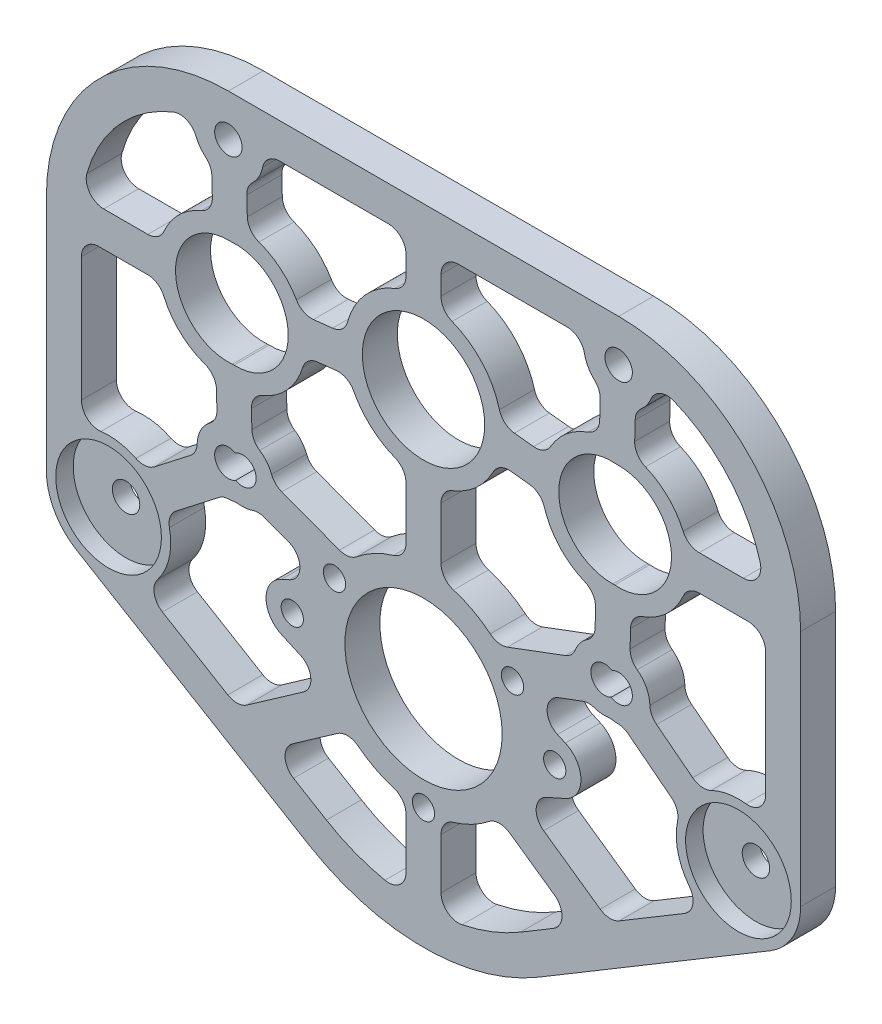
SolidWorks part; units mm, degrees
ref_plane "Front Plane" through (0, 0, 0) normal (0, 0, 1) x (1, 0, 0)
ref_plane "Top Plane" through (0, 0, 0) normal (0, 1, 0) x (1, 0, 0)
ref_plane "Right Plane" through (0, 0, 0) normal (1, 0, 0) x (0, 0, -1)
ref_plane "Plane1" through (0, 0, 3.175) normal (0, 0, 1) x (1, 0, 0)
sketch "Sketch1" plane through (0, 0, 3.175) normal (0, 0, 1) x (1, 0, 0)
  line L0 (0, -94.4087) -> (68.4315, -53.4351)
  line L1 (68.4315, -53.4351) -> (68.4315, 29.21)
  line L2 (68.4315, 29.21) -> (-68.4315, 29.21)
  line L3 (-68.4315, 29.21) -> (-68.4315, -53.4351)
  line L4 (-68.4315, -53.4351) -> (0, -94.4087)
extrude "Boss-Extrude1" add sketch "Sketch1" against normal blind 6.35
hole_wizard "M18 Clearance Hole1" positions "Sketch3" profile "Sketch2" hole size "M18" standard "ANSI Metric"
sketch "Sketch3" plane through (0, 0, 3.175) normal (0, 0, 1) x (1, 0, 0)
  point P0 (34.1324, -3.7778)
sketch "Sketch2" plane through (34.1324, -3.7778, 3.175) normal (1, 0, 0) x (0, -1, 0)
  line L0 (0, 0) -> (0, 6.35)
  line L1 (0, 6.35) -> (9.5885, 6.35)
  line L2 (9.5885, 6.35) -> (9.5885, 0)
  line L5 (9.5885, 0) -> (0, 0)
  line L10 (0, 6.35) -> (-9.5885, 6.35) construction
  line L11 (0, -6.35) -> (0, 107.95) construction
  dimension "Hole Dia." = 19.177
  dimension "Hole Depth" = 6.35
  dimension "Drill Angle" = 180
hole_wizard "M18 Clearance Hole2" positions "Sketch5" profile "Sketch4" hole size "M18" standard "ANSI Metric"
sketch "Sketch5" plane through (0, 0, 3.175) normal (0, 0, 1) x (1, 0, 0)
  point P0 (-34.1324, -3.7778)
sketch "Sketch4" plane through (-34.1324, -3.7778, 3.175) normal (1, 0, 0) x (0, -1, 0)
  line L0 (0, 0) -> (0, 6.35)
  line L1 (0, 6.35) -> (9.5885, 6.35)
  line L2 (9.5885, 6.35) -> (9.5885, 0)
  line L5 (9.5885, 0) -> (0, 0)
  line L10 (0, 6.35) -> (-9.5885, 6.35) construction
  line L11 (0, -6.35) -> (0, 107.95) construction
  dimension "Hole Dia." = 19.177
  dimension "Hole Depth" = 6.35
  dimension "Drill Angle" = 180
sketch "Sketch6" plane through (0, 0, 3.175) normal (0, 0, 1) x (1, 0, 0)
  line L0 (17.6151, -76.4604) -> (23.5825, -72.8874)
  line L1 (23.7726, -67.5625) -> (13.5655, -60.4154)
  line L2 (3.175, -65.8244) -> (3.175, -81.1835)
  arc A0 (3.175, -81.1835) -> (17.6151, -76.4604) centre (0, -47.0408) ccw
  arc A1 (23.5825, -72.8874) -> (23.7726, -67.5625) centre (21.9515, -70.1633) ccw
  arc A2 (13.5655, -60.4154) -> (3.175, -65.8244) centre (0, -47.0408) cw
extrude "Cut-Extrude1" cut sketch "Sketch6" against normal through all
sketch "Sketch7" plane through (0, 0, 3.175) normal (0, 0, 1) x (1, 0, 0)
  line L0 (31.913, 8.7913) -> (32.099, 16.1725)
  line L1 (29.1898, 22.86) -> (3.175, 22.86)
  line L2 (3.175, 22.86) -> (3.175, 13.9172)
  line L3 (14.1795, 1.6468) -> (22.2069, 0.7709)
  arc A0 (22.2069, 0.7709) -> (31.913, 8.7913) centre (34.1324, -3.7778) cw
  arc A1 (32.099, 16.1725) -> (29.1898, 22.86) centre (35.4115, 21.59) cw
  arc A2 (3.175, 13.9172) -> (14.1795, 1.6468) centre (0, 0) cw
extrude "Cut-Extrude2" cut sketch "Sketch7" against normal through all
sketch "Sketch8" plane through (0, 0, 3.175) normal (0, 0, 1) x (1, 0, 0)
  line L0 (13.4359, -33.536) -> (27.2428, -28.3669)
  line L1 (31.0928, -23.7619) -> (31.2829, -16.2191)
  line L2 (21.4909, -5.5387) -> (13.4908, -4.6658)
  line L3 (3.175, -13.9172) -> (3.175, -28.2572)
  arc A0 (3.175, -28.2572) -> (13.4359, -33.536) centre (0, -47.0408) cw
  arc A1 (27.2428, -28.3669) -> (31.0928, -23.7619) centre (32.8532, -29.1455) cw
  arc A2 (31.2829, -16.2191) -> (21.4909, -5.5387) centre (34.1324, -3.7778) cw
  arc A3 (13.4908, -4.6658) -> (3.175, -13.9172) centre (0, 0) cw
extrude "Cut-Extrude3" cut sketch "Sketch8" against normal through all
sketch "Sketch9" plane through (0, 0, 3.175) normal (0, 0, 1) x (1, 0, 0)
  line L0 (62.0815, -6.985) -> (47.776, -6.9766)
  line L1 (37.6309, -16.3791) -> (37.4408, -23.9218)
  line L2 (40.9401, -30.442) -> (50.5443, -37.8955)
  line L3 (62.0815, -36.8942) -> (62.0815, -6.985)
  arc A0 (47.776, -6.9766) -> (37.6309, -16.3791) centre (35.4115, -3.81) cw
  arc A1 (37.4408, -23.9218) -> (40.9401, -30.442) centre (35.4115, -29.21) cw
  arc A2 (50.5443, -37.8955) -> (62.0815, -36.8942) centre (57.15, -47.0408) cw
extrude "Cut-Extrude4" cut sketch "Sketch9" against normal through all
sketch "Sketch10" plane through (0, 0, 3.175) normal (0, 0, 1) x (1, 0, 0)
  line L0 (47.7716, -0.6266) -> (58.0296, -0.6326)
  line L1 (38.447, 16.0125) -> (38.261, 8.6314)
  arc A0 (38.261, 8.6314) -> (47.7716, -0.6266) centre (35.4115, -3.81) cw
  arc A1 (58.0296, -0.6326) -> (61.0882, 3.4008) centre (58.0315, 2.5424) ccw
  arc A2 (61.0882, 3.4008) -> (41.7412, 22.098) centre (35.4115, -3.81) ccw
  arc A3 (41.7412, 22.098) -> (38.447, 16.0125) centre (35.4115, 21.59) cw
extrude "Cut-Extrude5" cut sketch "Sketch10" against normal through all
sketch "Sketch11" plane through (0, 0, 3.175) normal (0, 0, 1) x (1, 0, 0)
  line L0 (-32.099, 16.1725) -> (-31.913, 8.7913)
  line L1 (-22.2069, 0.7709) -> (-14.1795, 1.6468)
  line L2 (-3.175, 13.9172) -> (-3.175, 22.86)
  line L3 (-3.175, 22.86) -> (-29.1898, 22.86)
  arc A0 (-29.1898, 22.86) -> (-32.099, 16.1725) centre (-35.4115, 21.59) cw
  arc A1 (-31.913, 8.7913) -> (-22.2069, 0.7709) centre (-34.1324, -3.7778) cw
  arc A2 (-14.1795, 1.6468) -> (-3.175, 13.9172) centre (0, 0) cw
extrude "Cut-Extrude6" cut sketch "Sketch11" against normal through all
sketch "Sketch12" plane through (0, 0, 3.175) normal (0, 0, 1) x (1, 0, 0)
  line L0 (-47.776, -6.9766) -> (-62.0815, -6.985)
  line L1 (-62.0815, -6.985) -> (-62.0815, -36.8942)
  line L2 (-50.5443, -37.8955) -> (-40.9401, -30.442)
  line L3 (-37.4408, -23.9218) -> (-37.6309, -16.3791)
  arc A0 (-37.6309, -16.3791) -> (-47.776, -6.9766) centre (-35.4115, -3.81) cw
  arc A1 (-62.0815, -36.8942) -> (-50.5443, -37.8955) centre (-57.15, -47.0408) cw
  arc A2 (-40.9401, -30.442) -> (-37.4408, -23.9218) centre (-35.4115, -29.21) cw
extrude "Cut-Extrude7" cut sketch "Sketch12" against normal through all
sketch "Sketch13" plane through (0, 0, 3.175) normal (0, 0, 1) x (1, 0, 0)
  line L0 (-38.261, 8.6314) -> (-38.447, 16.0125)
  line L1 (-58.0296, -0.6326) -> (-47.7716, -0.6266)
  arc A0 (-47.7716, -0.6266) -> (-38.261, 8.6314) centre (-35.4115, -3.81) cw
  arc A1 (-38.447, 16.0125) -> (-41.7412, 22.098) centre (-35.4115, 21.59) cw
  arc A2 (-41.7412, 22.098) -> (-61.0882, 3.4008) centre (-35.4115, -3.81) ccw
  arc A3 (-61.0882, 3.4008) -> (-58.0296, -0.6326) centre (-58.0315, 2.5424) ccw
extrude "Cut-Extrude8" cut sketch "Sketch13" against normal through all
sketch "Sketch14" plane through (0, 0, 3.175) normal (0, 0, 1) x (1, 0, 0)
  line L0 (-27.2428, -28.3669) -> (-13.4359, -33.536)
  line L1 (-3.175, -28.2572) -> (-3.175, -13.9172)
  line L2 (-13.4908, -4.6658) -> (-21.4909, -5.5387)
  line L3 (-31.2829, -16.2191) -> (-31.0928, -23.7619)
  arc A0 (-31.0928, -23.7619) -> (-27.2428, -28.3669) centre (-32.8532, -29.1455) cw
  arc A1 (-13.4359, -33.536) -> (-3.175, -28.2572) centre (0, -47.0408) cw
  arc A2 (-3.175, -13.9172) -> (-13.4908, -4.6658) centre (0, 0) cw
  arc A3 (-21.4909, -5.5387) -> (-31.2829, -16.2191) centre (-34.1324, -3.7778) cw
extrude "Cut-Extrude9" cut sketch "Sketch14" against normal through all
sketch "Sketch15" plane through (0, 0, 3.175) normal (0, 0, 1) x (1, 0, 0)
  line L0 (-13.5655, -60.4154) -> (-23.7726, -67.5625)
  line L1 (-23.5825, -72.8874) -> (-17.6151, -76.4604)
  line L2 (-3.175, -81.1835) -> (-3.175, -65.8244)
  arc A0 (-3.175, -65.8244) -> (-13.5655, -60.4154) centre (0, -47.0408) cw
  arc A1 (-23.7726, -67.5625) -> (-23.5825, -72.8874) centre (-21.9515, -70.1633) ccw
  arc A2 (-17.6151, -76.4604) -> (-3.175, -81.1835) centre (0, -47.0408) ccw
extrude "Cut-Extrude10" cut sketch "Sketch15" against normal through all
sketch "Sketch16" plane through (0, 0, 3.175) normal (0, 0, 1) x (1, 0, 0)
  line L0 (-22.3189, -52.9267) -> (-25.7577, -51.3879)
  line L1 (-25.7473, -42.689) -> (-24.3147, -42.0521)
  line L2 (-24.4913, -36.1774) -> (-30.0808, -34.0848)
  line L3 (-36.2193, -34.8163) -> (-46.6512, -42.912)
  line L4 (-50.978, -56.4842) -> (-33.7521, -66.7983)
  line L5 (-33.7521, -66.7983) -> (-21.7946, -58.4256)
  arc A0 (-21.7946, -58.4256) -> (-22.3189, -52.9267) centre (-23.6157, -55.8248) ccw
  arc A1 (-25.7577, -51.3879) -> (-25.7473, -42.689) centre (-23.8125, -47.0408) cw
  arc A2 (-24.3147, -42.0521) -> (-24.4913, -36.1774) centre (-25.6045, -39.1509) ccw
  arc A3 (-30.0808, -34.0848) -> (-33.9934, -34.6938) centre (-32.8532, -29.1455) cw
  arc A4 (-33.9934, -34.6938) -> (-36.2193, -34.8163) centre (-35.4115, -29.21) cw
  arc A5 (-46.6512, -42.912) -> (-50.978, -56.4842) centre (-57.15, -47.0408) cw
extrude "Cut-Extrude11" cut sketch "Sketch16" against normal through all
sketch "Sketch17" plane through (0, 0, -3.175) normal (0, 0, -1) x (-1, 0, 0)
  line L0 (-33.7521, -66.7983) -> (-21.7946, -58.4256)
  line L1 (-22.3189, -52.9267) -> (-25.7577, -51.3879)
  line L2 (-25.7473, -42.689) -> (-24.3147, -42.0521)
  line L3 (-24.4913, -36.1774) -> (-30.0808, -34.0848)
  line L4 (-36.2193, -34.8163) -> (-46.6512, -42.912)
  line L5 (-50.978, -56.4842) -> (-33.7521, -66.7983)
  arc A0 (-21.7946, -58.4256) -> (-22.3189, -52.9267) centre (-23.6157, -55.8248) ccw
  arc A1 (-25.7577, -51.3879) -> (-25.7473, -42.689) centre (-23.8125, -47.0408) cw
  arc A2 (-24.3147, -42.0521) -> (-24.4913, -36.1774) centre (-25.6045, -39.1509) ccw
  arc A3 (-30.0808, -34.0848) -> (-33.9934, -34.6938) centre (-32.8532, -29.1455) cw
  arc A4 (-33.9934, -34.6938) -> (-36.2193, -34.8163) centre (-35.4115, -29.21) cw
  arc A5 (-46.6512, -42.912) -> (-50.978, -56.4842) centre (-57.15, -47.0408) cw
extrude "Cut-Extrude12" cut sketch "Sketch17" against normal through all
ref_plane "Plane2" through (0, -3.81, 0) normal (0, 1, 0) x (1, 0, 0)
sketch "Sketch18" plane through (0, -3.81, 0) normal (0, 1, 0) x (1, 0, 0)
  line L0 (45, 3.175) -> (35.4115, 3.175)
  line L1 (35.4115, 3.175) -> (35.4115, -3.175)
  line L2 (35.4115, -3.175) -> (45, -3.175)
  line L3 (45, -3.175) -> (45, 3.175)
  line L4 (35.4115, 3.175) -> (35.4115, -3.175) construction
revolve "Cut-Revolve1" cut sketch "Sketch18" angle 360 about L4
ref_plane "Plane3" through (0, -3.81, 0) normal (0, -1, 0) x (1, 0, 0)
sketch "Sketch19" plane through (0, -3.81, 0) normal (0, -1, 0) x (1, 0, 0)
  line L0 (-25.823, 3.175) -> (-35.4115, 3.175)
  line L1 (-35.4115, 3.175) -> (-35.4115, -3.175)
  line L2 (-35.4115, -3.175) -> (-25.823, -3.175)
  line L3 (-25.823, -3.175) -> (-25.823, 3.175)
  line L4 (-35.4115, 3.175) -> (-35.4115, -3.175) construction
revolve "Cut-Revolve2" cut sketch "Sketch19" angle 360 about L4
hole_wizard "M25 Clearance Hole1" positions "Sketch21" profile "Sketch20" hole size "M25" standard "ANSI Metric"
sketch "Sketch21" plane through (0, 0, 3.175) normal (0, 0, 1) x (1, 0, 0)
  point P0 (0, -47.0408)
sketch "Sketch20" plane through (0, -47.0408, 3.175) normal (1, 0, 0) x (0, -1, 0)
  line L0 (0, 0) -> (0, 6.35)
  line L1 (0, 6.35) -> (14.2748, 6.35)
  line L2 (14.2748, 6.35) -> (14.2748, 0)
  line L5 (14.2748, 0) -> (0, 0)
  line L11 (0, -6.35) -> (0, 107.95) construction
  dimension "Thru Hole Dia." = 28.5496
  dimension "Thru Hole Depth" = 6.35
hole_wizard "Hole1" positions "Sketch23" profile "Sketch22" legacy
sketch "Sketch23" plane through (0, 0, 3.175) normal (0, 0, 1) x (1, 0, 0)
  point P0 (35.4115, -29.21)
  point P1 (-32.8532, -29.1455)
  point P2 (-35.4115, 21.59)
  point P3 (35.4115, 21.59)
sketch "Sketch22" plane through (35.4115, -29.21, 3.175) normal (1, 0, 0) x (0, -1, 0)
  line L0 (0, 0) -> (0, 6.35)
  line L1 (0, 6.35) -> (2.4892, 6.35)
  line L2 (2.4892, 6.35) -> (2.4892, 0)
  line L3 (2.4892, 0) -> (0, 0)
  line L4 (0, 110) -> (0, -10) construction
  dimension "Diameter" = 4.9784
  dimension "Depth" = 6.35
hole_wizard "Hole2" positions "Sketch25" profile "Sketch24" legacy
sketch "Sketch25" plane through (0, 0, -3.175) normal (0, 0, -1) x (-1, 0, 0)
  point P0 (-32.8532, -29.1455)
  point P1 (35.4115, -29.21)
sketch "Sketch24" plane through (32.8532, -29.1455, -3.175) normal (1, 0, 0) x (0, 1, 0)
  line L0 (0, 0) -> (0, 6.35)
  line L1 (0, 6.35) -> (2.4892, 6.35)
  line L2 (2.4892, 6.35) -> (2.4892, 0)
  line L3 (2.4892, 0) -> (0, 0)
  line L4 (0, 110) -> (0, -10) construction
  dimension "Diameter" = 4.9784
  dimension "Depth" = 6.35
hole_wizard "M20 Clearance Hole1" positions "Sketch27" profile "Sketch26" hole size "M20" standard "ANSI Metric"
sketch "Sketch27" plane through (0, 0, 3.175) normal (0, 0, 1) x (1, 0, 0)
  point P0 (0, 0)
sketch "Sketch26" plane through (0, 0, 3.175) normal (1, 0, 0) x (0, -1, 0)
  line L0 (0, 0) -> (0, 6.35)
  line L1 (0, 6.35) -> (11.0998, 6.35)
  line L2 (11.0998, 6.35) -> (11.0998, 0)
  line L5 (11.0998, 0) -> (0, 0)
  line L11 (0, -6.35) -> (0, 107.95) construction
  dimension "Thru Hole Dia." = 22.1996
  dimension "Thru Hole Depth" = 6.35
hole_wizard "M3.5 Clearance Hole1" positions "Sketch29" profile "Sketch28" hole size "M3.5" standard "ANSI Metric"
sketch "Sketch29" plane through (0, 0, 3.175) normal (0, 0, 1) x (1, 0, 0)
  point P0 (0, -65.6939)
  point P1 (-16.1541, -37.7142)
  point P2 (16.1541, -37.7142)
  point P3 (-23.8125, -47.0408)
  point P4 (23.8125, -47.0408)
sketch "Sketch28" plane through (0, -65.6939, 3.175) normal (1, 0, 0) x (0, -1, 0)
  line L0 (0, 0) -> (0, 6.35)
  line L1 (0, 6.35) -> (2.0193, 6.35)
  line L2 (2.0193, 6.35) -> (2.0193, 0)
  line L5 (2.0193, 0) -> (0, 0)
  line L11 (0, -6.35) -> (0, 107.95) construction
  dimension "Thru Hole Dia." = 4.0386
  dimension "Thru Hole Depth" = 6.35
hole_wizard "Hole3" positions "Sketch31" profile "Sketch30" legacy
sketch "Sketch31" plane through (0, 0, 3.175) normal (0, 0, 1) x (1, 0, 0)
  point P0 (57.15, -47.0408)
  point P1 (-57.15, -47.0408)
sketch "Sketch30" plane through (57.15, -47.0408, 3.175) normal (1, 0, 0) x (0, -1, 0)
  line L0 (0, 0) -> (0, 6.35)
  line L1 (0, 6.35) -> (2.4892, 6.35)
  line L2 (2.4892, 6.35) -> (2.4892, 3.175)
  line L3 (2.4892, 3.175) -> (9.5885, 3.175)
  line L4 (9.5885, 3.175) -> (9.5885, 0)
  line L5 (9.5885, 0) -> (0, 0)
  line L6 (0, 110) -> (0, -10) construction
  dimension "Diameter" = 4.9784
  dimension "Depth" = 6.35
  dimension "C-Bore Diameter" = 19.177
  dimension "C-Bore Depth" = 3.175
fillet "Fillet1" radius 3.175 74 edges at (3.175, 22.86, 0) (41.7412, 22.098, 0) (-31.913, 8.7913, 0) (36.2193, -34.8163, 0) (31.2829, -16.2191, 0) (46.6512, -42.912, 0) (-40.9401, -30.442, 0) (50.978, -56.4842, 0) (-3.175, 13.9172, 0) (-46.6512, -42.912, 0) (62.0815, -6.985, 0) (-36.2193, -34.8163, 0) (3.175, -28.2572, 0) (-30.0808, -34.0848, 0) (30.0808, -34.0848, 0) (-33.7521, -66.7983, 0) (-14.1795, 1.6468, 0) (-50.978, -56.4842, 0) (-29.1898, 22.86, 0) (-3.175, -65.8244, 0) (38.261, 8.6314, 0) (-3.175, -81.1835, 0) (37.6309, -16.3791, 0) (-33.9934, -34.6938, 0) (50.5443, -37.8955, 0) (-13.5655, -60.4154, 0) (27.2428, -28.3669, 0) (-3.175, -13.9172, 0) (13.4908, -4.6658, 0) (-3.175, -28.2572, 0) (32.099, 16.1725, 0) (-13.4359, -33.536, 0) (-37.4408, -23.9218, 0) (-27.2428, -28.3669, 0) (-50.5443, -37.8955, 0) (-31.0928, -23.7619, 0) (-22.2069, 0.7709, 0) (-31.2829, -16.2191, 0) (-32.099, 16.1725, 0) (-21.4909, -5.5387, 0) (-3.175, 22.86, 0) (-13.4908, -4.6658, 0) (47.7716, -0.6266, 0) (-38.447, 16.0125, 0) (38.447, 16.0125, 0) (-38.261, 8.6314, 0) (37.4408, -23.9218, 0) (-47.7716, -0.6266, 0) (47.776, -6.9766, 0) (-41.7412, 22.098, 0) (62.0815, -36.8942, 0) (-34.531, -13.358, 0) (-35.0129, 5.7702, 0) (40.9401, -30.442, 0) (31.0928, -23.7619, 0) (35.0129, 5.7702, 0) (34.531, -13.358, 0) (13.4359, -33.536, 0) (3.175, -13.9172, 0) (22.2069, 0.7709, 0) (21.4909, -5.5387, 0) (14.1795, 1.6468, 0) (29.1898, 22.86, 0) (33.7521, -66.7983, 0) (31.913, 8.7913, 0) (3.175, -65.8244, 0) (33.9934, -34.6938, 0) (3.175, 13.9172, 0) (-62.0815, -36.8942, 0) (3.175, -81.1835, 0) (-62.0815, -6.985, 0) (13.5655, -60.4154, 0) (-47.776, -6.9766, 0) (-37.6309, -16.3791, 0)
fillet "Fillet2" radius 11.2815 2 edges at (-68.4315, -53.4351, 0) (68.4315, -53.4351, 0)
fillet "Fillet3" radius 33.02 2 edges at (-68.4315, 29.21, 0) (68.4315, 29.21, 0)
fillet "Fillet4" radius 40.64 1 edges at (0, -94.4087, 0)
